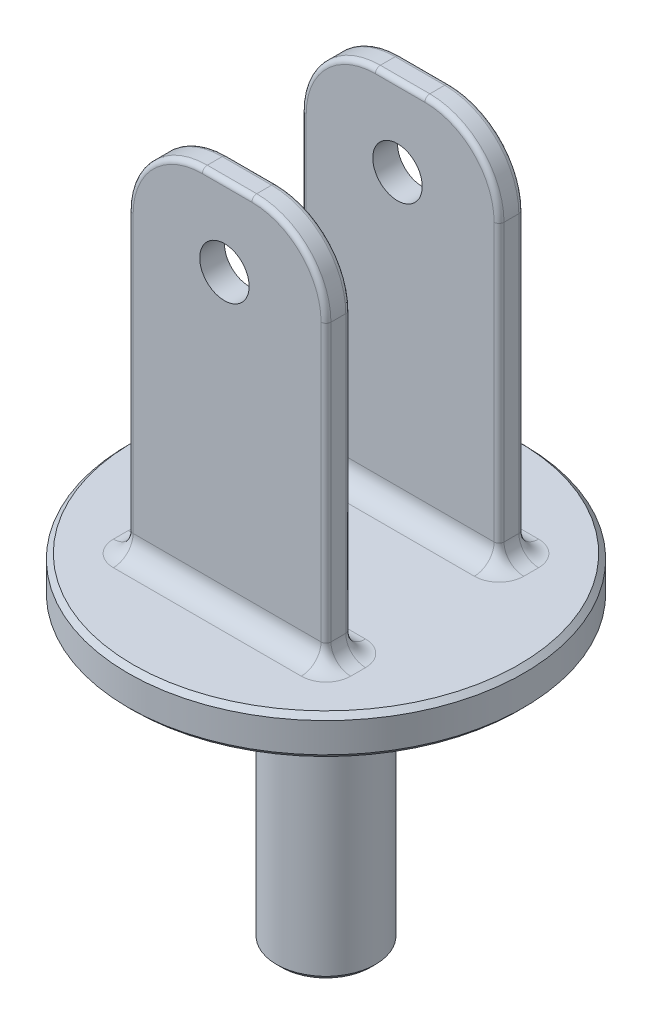
SolidWorks part; units mm, degrees
ref_plane "Front Plane" through (0, 0, 0) normal (0, 0, 1) x (1, 0, 0)
ref_plane "Top Plane" through (0, 0, 0) normal (0, 1, 0) x (1, 0, 0)
ref_plane "Right Plane" through (0, 0, 0) normal (1, 0, 0) x (0, 0, -1)
sketch "Sketch2" plane through (0, 0, 0) normal (0, 1, 0) x (1, 0, 0)
  circle A0 centre (0, 0) radius 40
  dimension "D1" = 80
extrude "Boss-Extrude1" add sketch "Sketch2" along normal blind 8
sketch "Sketch6" plane through (0, 0, 0) normal (0, -1, 0) x (1, 0, 0)
  circle A0 centre (0, 0) radius 10
  circle A1 centre (0, 0) radius 7.5
  dimension "D1" = 20
  dimension "D2" = 15
extrude "Boss-Extrude4" add sketch "Sketch6" along normal blind 60
chamfer "Chamfer1" distance 1 angle 45 3 edges at (0, 0, 40) (0, 8, 40) (0, -60, -10)
sketch "Sketch20" plane through (0, 0, 0) normal (0, 0, 1) x (1, 0, 0)
  line L0 (0, 0) -> (-34.9854, 147.6672) construction
sketch "Sketch19" plane through (0, 8, 0) normal (0, 1, 0) x (1, 0, 0)
  line L0 (0, 0) -> (0, 39) construction
  line L2 (20, 20) -> (-20, 20)
  line L3 (20, 20) -> (20, 15)
  line L4 (20, 15) -> (-20, 15)
  line L5 (-20, 20) -> (-20, 15)
  line L6 (20, 20) -> (-20, 15) construction
  line L7 (20, 15) -> (-20, 20) construction
  circle A0 centre (0, 0) radius 39 construction
  point P6 (0, 17.5)
  dimension "D1" = 40
  dimension "D2" = 15
  dimension "D3" = 5
extrude "Boss-Extrude5" add sketch "Sketch19" along normal blind 75
fillet "Fillet1" radius 15 2 edges at (20, 83, -17.5) (-20, 83, -17.5)
fillet "Fillet2" radius 1 10 edges at (20, 38, -20) (15.6066, 78.6066, -20) (0, 83, -20) (-15.6066, 78.6066, -20) (20, 38, -15) (15.6066, 78.6066, -15) (0, 83, -15) (-15.6066, 78.6066, -15) (-20, 38, -20) (-20, 38, -15)
fillet "Fillet3" radius 4 8 edges at (-19.7071, 8, -15.2929) (-20, 8, -17.5) (-19.7071, 8, -19.7071) (0, 8, -20) (19.7071, 8, -19.7071) (20, 8, -17.5) (19.7071, 8, -15.2929) (0, 8, -15)
mirror "Mirror2" about plane through (0, 0, 0) normal (0, 0, 1) of "Boss-Extrude5", "Fillet1", "Fillet2", "Fillet3"
sketch "Sketch21" plane through (0, 0, 20) normal (0, 0, 1) x (1, 0, 0)
  line L0 (5, 82) -> (-5, 82) construction
  line L1 (-19, 68) -> (-19, 12) construction
  line L2 (19, 12) -> (19, 68) construction
  circle A0 centre (-0.54, 67) radius 5
  dimension "D1" = 10
  dimension "D2" = 15
  dimension "D3" = 18.46
  dimension "D4" = 19.54
extrude "Cut-Extrude1" cut sketch "Sketch21" against normal up to surface (40 mm away) up to face at (0, 54.9665, -20)
